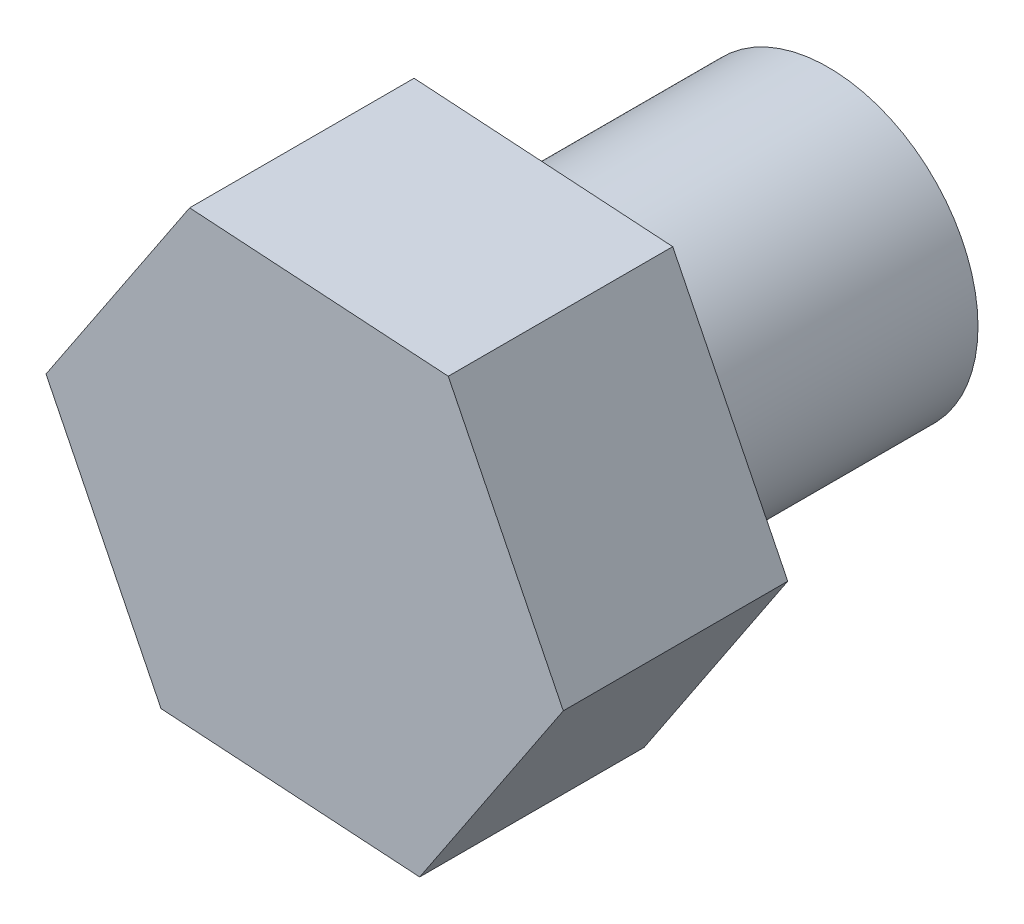
SolidWorks part; units mm, degrees
ref_plane "前视基准面" through (0, 0, 0) normal (0, 0, 1) x (1, 0, 0)
ref_plane "上视基准面" through (0, 0, 0) normal (0, 1, 0) x (1, 0, 0)
ref_plane "右视基准面" through (0, 0, 0) normal (1, 0, 0) x (0, 0, -1)
sketch "草图1" plane through (0, 0, 0) normal (0, 0, 1) x (1, 0, 0)
  line L1 (1.5374, -3.1043) -> (3.4571, -0.2207)
  line L2 (3.4571, -0.2207) -> (1.9197, 2.8835)
  line L3 (1.9197, 2.8835) -> (-1.5374, 3.1043)
  line L4 (-1.5374, 3.1043) -> (-3.4571, 0.2207)
  line L5 (-3.4571, 0.2207) -> (-1.9197, -2.8835)
  line L6 (-1.9197, -2.8835) -> (1.5374, -3.1043)
  circle A0 centre (0, 0) radius 3 construction
  dimension "D1" = 6
extrude "凸台-拉伸1" add sketch "草图1" along normal blind 3
sketch "草图2" plane through (0, 0, 0) normal (0, 0, -1) x (-1, 0, 0)
  circle A0 centre (0, 0) radius 2
extrude "凸台-拉伸2" add sketch "草图2" along normal blind 4
